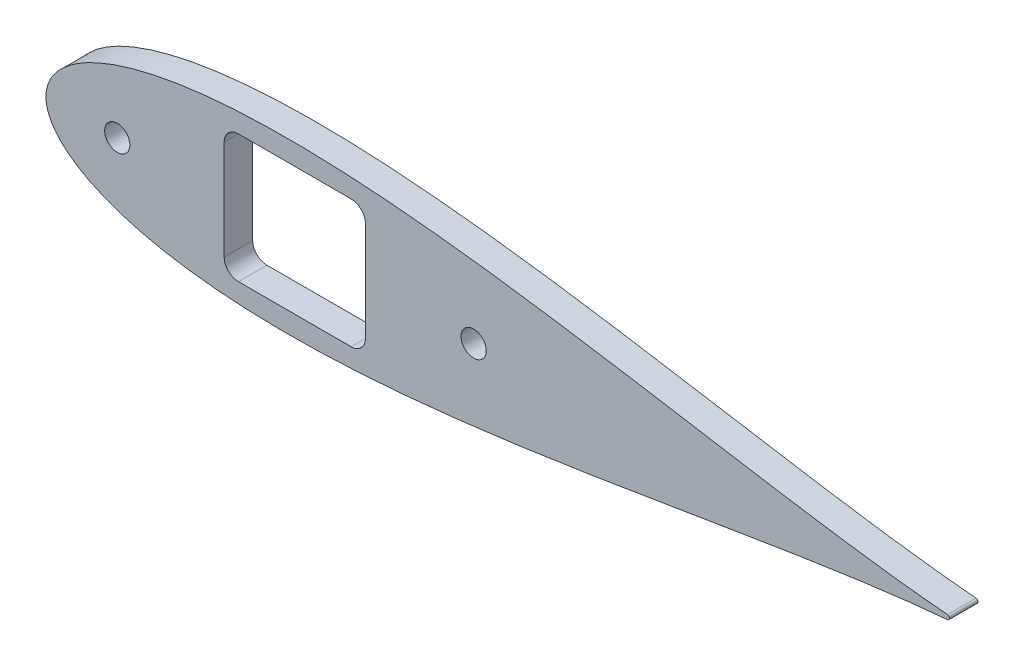
SolidWorks part; units mm, degrees
ref_plane "Front Plane" through (0, 0, 0) normal (0, 0, 1) x (1, 0, 0)
ref_plane "Top Plane" through (0, 0, 0) normal (0, 1, 0) x (1, 0, 0)
ref_plane "Right Plane" through (0, 0, 0) normal (1, 0, 0) x (0, 0, -1)
curve "Curve4"
  spline degree 3 poles (100, 0, 0) (99.8498, 0.0023, 0) (99.4759, 0.008, 0) (99.1023, 0.0238, 0) (98.8789, 0.0332, 0) knots 0 0 0 0 0.401829 1 1 1 1
curve "Curve5"
  spline degree 3 poles (99.3714, -0.0082, 0) (100.2526, 0, 0) (99.3714, 0.0082, 0) (98.8504, 0.035, 0) (97.904, 0.0811, 0) (96.8285, 0.1543, 0) (95.5159, 0.2583, 0) (94.013, 0.3972, 0) (92.313, 0.574, 0) (90.4281, 0.791, 0) (88.3655, 1.0495, 0) (86.1348, 1.3497, 0) (83.7456, 1.691, 0) (81.2082, 2.0715, 0) (78.5335, 2.4886, 0) (75.7326, 2.9386, 0) (72.8172, 3.4168, 0) (69.799, 3.9177, 0) (66.6904, 4.435, 0) (63.5039, 4.9616, 0) (60.2521, 5.4899, 0) (56.948, 6.0119, 0) (53.6049, 6.519, 0) (50.2363, 7.0024, 0) (46.8558, 7.4534, 0) (43.4774, 7.8632, 0) (40.1152, 8.2232, 0) (36.7837, 8.5249, 0) (33.4975, 8.7606, 0) (30.2716, 8.923, 0) (27.1211, 9.0055, 0) (24.0614, 9.0025, 0) (21.108, 8.909, 0) (18.277, 8.7213, 0) (15.5843, 8.4369, 0) (13.0466, 8.0543, 0) (10.6806, 7.5735, 0) (8.5039, 6.996, 0) (6.5349, 6.3253, 0) (4.7933, 5.5673, 0) (3.3001, 4.7321, 0) (2.0777, 3.8366, 0) (1.1467, 2.91, 0) (0.5165, 2.0014, 0) (0.165, 1.1816, 0) (0.0231, 0.524, 0) (-0.0093, 0, 0) (0.0231, -0.524, 0) (0.165, -1.1816, 0) (0.5165, -2.0014, 0) (1.1467, -2.91, 0) (2.0777, -3.8366, 0) (3.3001, -4.7321, 0) (4.7933, -5.5673, 0) (6.5349, -6.3253, 0) (8.5039, -6.996, 0) (10.6806, -7.5735, 0) (13.0466, -8.0543, 0) (15.5843, -8.4369, 0) (18.277, -8.7213, 0) (21.108, -8.909, 0) (24.0614, -9.0025, 0) (27.1211, -9.0055, 0) (30.2716, -8.923, 0) (33.4975, -8.7606, 0) (36.7837, -8.5249, 0) (40.1152, -8.2232, 0) (43.4774, -7.8632, 0) (46.8558, -7.4534, 0) (50.2363, -7.0024, 0) (53.6049, -6.519, 0) (56.948, -6.0119, 0) (60.2521, -5.4899, 0) (63.5039, -4.9616, 0) (66.6904, -4.435, 0) (69.799, -3.9177, 0) (72.8172, -3.4168, 0) (75.7326, -2.9386, 0) (78.5335, -2.4886, 0) (81.2082, -2.0715, 0) (83.7456, -1.691, 0) (86.1348, -1.3497, 0) (88.3655, -1.0495, 0) (90.4281, -0.791, 0) (92.313, -0.574, 0) (94.013, -0.3972, 0) (95.5159, -0.2583, 0) (96.8285, -0.1543, 0) (97.904, -0.0811, 0) (98.8504, -0.035, 0) (99.3714, -0.0082, 0) (100.2526, 0, 0) (99.3714, 0.0082, 0) knots -0.009667 -0.005395 -0.002168 0 0.002168 0.005395 0.009667 0.014967 0.021271 0.028553 0.036781 0.04592 0.055932 0.066773 0.078397 0.090755 0.103793 0.117456 0.131686 0.146422 0.1616 0.177156 0.193024 0.209135 0.225421 0.241812 0.258238 0.274629 0.290914 0.307025 0.322893 0.338448 0.353626 0.368361 0.38259 0.396253 0.40929 0.421647 0.43327 0.444109 0.454119 0.463255 0.471479 0.478755 0.485052 0.490344 0.49461 0.497833 0.5 0.502167 0.50539 0.509656 0.514948 0.521245 0.528521 0.536745 0.545881 0.555891 0.56673 0.578353 0.59071 0.603747 0.61741 0.631639 0.646374 0.661552 0.677107 0.692975 0.709086 0.725371 0.741762 0.758188 0.774579 0.790865 0.806976 0.822844 0.8384 0.853578 0.868314 0.882544 0.896207 0.909245 0.921603 0.933227 0.944068 0.95408 0.963219 0.971447 0.978729 0.985033 0.990333 0.994605 0.997832 1 1.002168 1.005395 1.009667 periodic
sketch "Sketch2" plane through (0, 0, 0) normal (0, 0, 1) x (1, 0, 0)
  line L0 (642.3793, 0) -> (0, 0) construction
  circle A14 centre (642.3793, 0) radius 1.5875 construction
  arc A15 (642.5108, -1.582) -> (642.5108, 1.582) centre (642.3793, 0) ccw
  spline S2 degree 3 poles (666.3448, -0.0547) (672.2538, 0) (666.3448, 0.0547) (662.8509, 0.2344) (656.505, 0.5436) (649.293, 1.0348) (640.4916, 1.7319) (630.4138, 2.6634) (619.0141, 3.8493) (606.375, 5.3044) (592.5439, 7.0376) (577.5855, 9.0506) (561.5643, 11.3389) (544.5497, 13.8907) (526.6141, 16.6877) (507.8326, 19.7051) (488.2827, 22.9117) (468.0444, 26.2704) (447.1994, 29.739) (425.8316, 33.2703) (404.0263, 36.8132) (381.8707, 40.3133) (359.4533, 43.7135) (336.8645, 46.9554) (314.1962, 49.9798) (291.5418, 52.7277) (268.9963, 55.1412) (246.6566, 57.1646) (224.6209, 58.7452) (202.9892, 59.8341) (181.8631, 60.3875) (161.3458, 60.367) (141.542, 59.7399) (122.5581, 58.4818) (104.5023, 56.5743) (87.485, 54.0089) (71.6197, 50.7848) (57.0237, 46.9125) (43.8205, 42.415) (32.1416, 37.3322) (22.1291, 31.7315) (13.9324, 25.7264) (7.6896, 19.5132) (3.4631, 13.4204) (1.1063, 7.9234) (0.1546, 3.5138) (-0.0622, 0) (0.1546, -3.5138) (1.1063, -7.9234) (3.4631, -13.4204) (7.6896, -19.5132) (13.9324, -25.7264) (22.1291, -31.7315) (32.1416, -37.3322) (43.8205, -42.415) (57.0237, -46.9125) (71.6197, -50.7848) (87.485, -54.0089) (104.5023, -56.5743) (122.5581, -58.4818) (141.542, -59.7399) (161.3458, -60.367) (181.8631, -60.3875) (202.9892, -59.8341) (224.6209, -58.7452) (246.6566, -57.1646) (268.9963, -55.1412) (291.5418, -52.7277) (314.1962, -49.9798) (336.8645, -46.9554) (359.4533, -43.7135) (381.8707, -40.3133) (404.0263, -36.8132) (425.8316, -33.2703) (447.1994, -29.739) (468.0444, -26.2704) (488.2827, -22.9117) (507.8326, -19.7051) (526.6141, -16.6877) (544.5497, -13.8907) (561.5643, -11.3389) (577.5855, -9.0506) (592.5439, -7.0376) (606.375, -5.3044) (619.0141, -3.8493) (630.4138, -2.6634) (640.4916, -1.7319) (649.293, -1.0348) (656.505, -0.5436) (662.8509, -0.2344) (666.3448, -0.0547) (672.2538, 0) (666.3448, 0.0547) knots -0.009667 -0.005395 -0.002168 0 0.002168 0.005395 0.009667 0.014967 0.021271 0.028553 0.036781 0.04592 0.055932 0.066773 0.078397 0.090755 0.103793 0.117456 0.131686 0.146422 0.1616 0.177156 0.193024 0.209135 0.225421 0.241812 0.258238 0.274629 0.290914 0.307025 0.322893 0.338448 0.353626 0.368361 0.38259 0.396253 0.40929 0.421647 0.43327 0.444109 0.454119 0.463255 0.471479 0.478755 0.485052 0.490344 0.49461 0.497833 0.5 0.502167 0.50539 0.509656 0.514948 0.521245 0.528521 0.536745 0.545881 0.555891 0.56673 0.578353 0.59071 0.603747 0.61741 0.631639 0.646374 0.661552 0.677107 0.692975 0.709086 0.725371 0.741762 0.758188 0.774579 0.790865 0.806976 0.822844 0.8384 0.853578 0.868314 0.882544 0.896207 0.909245 0.921603 0.933227 0.944068 0.95408 0.963219 0.971447 0.978729 0.985033 0.990333 0.994605 0.997832 1 1.002168 1.005395 1.009667 only from (670.56, 0) to (670.56, 0)
  point P8 (1.2169, -4.6585)
  point P10 (1.2169, 4.6585)
  dimension "D10" = 3.175
extrude "Boss-Extrude1" add sketch "Sketch2" along normal blind 5.4737
extrude "Cut-Extrude4" [suppressed] cut sketch "Sketch7" against normal through all
sketch "Sketch7" plane through (327.9592, -13.7514, 6.35) normal (0, 0, 1) x (1, 0, 0)
  line L1 (-154.9852, -16.7286) -> (-66.0852, -16.7286)
  line L2 (-154.9852, -16.7286) -> (-154.9852, 44.2314)
  line L3 (-154.9852, 44.2314) -> (-66.0852, 44.2314)
  line L4 (-66.0852, -16.7286) -> (-66.0852, 44.2314)
  line L5 (-154.9852, -16.7286) -> (-66.0852, 44.2314) construction
  line L6 (-154.9852, 44.2314) -> (-66.0852, -16.7286) construction
  point P0 (-110.5352, 13.7514)
extrude "Cut-Extrude5" [suppressed] cut sketch "Sketch8" against normal through all
sketch "Sketch8" plane through (327.9592, -13.7514, 6.35) normal (0, 0, 1) x (1, 0, 0)
  circle A0 centre (314.9285, 13.7514) radius 1.2446
scale "Scale1" bodies to scale 101 scale about origin uniform scaling yes scale factor 0.25
sketch "Sketch11" plane through (0, 0, 0) normal (0, 0, -1) x (-1, 0, 0)
  arc A1 (-160.6277, 0.3955) -> (-160.6277, -0.3955) centre (-160.5948, 0) ccw
  arc A2 (-160.6277, 0.3955) -> (-160.6277, -0.3955) centre (-160.5948, 0) ccw
  spline S1 degree 3 poles (2828.4979, -252.2208) (-262.9609, -9.0876) (-204.7793, 3.6945) (-157.6035, -0.6658) (-154.7535, -0.9623) (-151.5937, -1.3261) (-148.136, -1.7594) (-144.3964, -2.2627) (-140.3911, -2.8347) (-136.1374, -3.4727) (-131.6535, -4.1719) (-126.9581, -4.9263) (-122.0707, -5.7279) (-117.0111, -6.5676) (-111.7999, -7.4348) (-106.4579, -8.3176) (-101.0066, -9.2033) (-95.4677, -10.0783) (-89.8633, -10.9284) (-84.2161, -11.7389) (-78.5491, -12.495) (-72.8854, -13.1819) (-67.2491, -13.7853) (-61.6641, -14.2912) (-56.1552, -14.6863) (-50.7473, -14.9585) (-45.4658, -15.0969) (-40.3365, -15.0917) (-35.3855, -14.935) (-30.6395, -14.6204) (-26.1256, -14.1436) (-21.8713, -13.5022) (-17.9049, -12.6962) (-14.2559, -11.7281) (-10.9551, -10.6038) (-8.0354, -9.3331) (-5.5323, -7.9329) (-3.4831, -6.4316) (-1.9224, -4.8783) (-0.8658, -3.3551) (-0.2766, -1.9808) (-0.0387, -0.8784) (0.0155, 0) (-0.0387, 0.8784) (-0.2766, 1.9808) (-0.8658, 3.3551) (-1.9224, 4.8783) (-3.4831, 6.4316) (-5.5323, 7.9329) (-8.0354, 9.3331) (-10.9551, 10.6038) (-14.2559, 11.7281) (-17.9049, 12.6962) (-21.8713, 13.5022) (-26.1256, 14.1436) (-30.6395, 14.6204) (-35.3855, 14.935) (-40.3365, 15.0917) (-45.4658, 15.0969) (-50.7473, 14.9585) (-56.1552, 14.6863) (-61.6641, 14.2912) (-67.2491, 13.7853) (-72.8854, 13.1819) (-78.5491, 12.495) (-84.2161, 11.7389) (-89.8633, 10.9284) (-95.4677, 10.0783) (-101.0066, 9.2033) (-106.4579, 8.3176) (-111.7999, 7.4348) (-117.0111, 6.5676) (-122.0707, 5.7279) (-126.9581, 4.9263) (-131.6535, 4.1719) (-136.1374, 3.4727) (-140.3911, 2.8347) (-144.3964, 2.2627) (-148.136, 1.7594) (-151.5937, 1.3261) (-154.7535, 0.9623) (-157.6035, 0.6658) (-204.7789, -3.6945) (-262.9599, 9.0874) (2828.4114, 252.214) knots -0.371679 -0.371679 -0.371679 -0.371679 0.021271 0.028553 0.036781 0.04592 0.055932 0.066773 0.078397 0.090755 0.103793 0.117456 0.131686 0.146422 0.1616 0.177156 0.193024 0.209135 0.225421 0.241812 0.258238 0.274629 0.290914 0.307025 0.322893 0.338448 0.353626 0.368361 0.38259 0.396253 0.40929 0.421647 0.43327 0.444109 0.454119 0.463255 0.471479 0.478755 0.485052 0.490344 0.49461 0.497833 0.5 0.502167 0.50539 0.509656 0.514948 0.521245 0.528521 0.536745 0.545881 0.555891 0.56673 0.578353 0.59071 0.603747 0.61741 0.631639 0.646374 0.661552 0.677107 0.692975 0.709086 0.725371 0.741762 0.758188 0.774579 0.790865 0.806976 0.822844 0.8384 0.853578 0.868314 0.882544 0.896207 0.909245 0.921603 0.933227 0.944068 0.95408 0.963219 0.971447 0.978729 1.371676 1.371676 1.371676 1.371676 only from (-160.6277, -0.3955) to (-160.6277, 0.3955)
  spline S2 degree 3 poles (-160.6277, -0.3955) (-160.4983, -0.4063) (-159.5234, -0.4884) (-157.6035, -0.6658) (-154.7535, -0.9623) (-151.5937, -1.3261) (-148.136, -1.7594) (-144.3964, -2.2627) (-140.3911, -2.8347) (-136.1374, -3.4727) (-131.6535, -4.1719) (-126.9581, -4.9263) (-122.0707, -5.7279) (-117.0111, -6.5676) (-111.7999, -7.4348) (-106.4579, -8.3176) (-101.0066, -9.2033) (-95.4677, -10.0783) (-89.8633, -10.9284) (-84.2161, -11.7389) (-78.5491, -12.495) (-72.8854, -13.1819) (-67.2491, -13.7853) (-61.6641, -14.2912) (-56.1552, -14.6863) (-50.7473, -14.9585) (-45.4658, -15.0969) (-40.3365, -15.0917) (-35.3855, -14.935) (-30.6395, -14.6204) (-26.1256, -14.1436) (-21.8713, -13.5022) (-17.9049, -12.6962) (-14.2559, -11.7281) (-10.9551, -10.6038) (-8.0354, -9.3331) (-5.5323, -7.9329) (-3.4831, -6.4316) (-1.9224, -4.8783) (-0.8658, -3.3551) (-0.2766, -1.9808) (-0.0387, -0.8784) (0.0155, 0) (-0.0387, 0.8784) (-0.2766, 1.9808) (-0.8658, 3.3551) (-1.9224, 4.8783) (-3.4831, 6.4316) (-5.5323, 7.9329) (-8.0354, 9.3331) (-10.9551, 10.6038) (-14.2559, 11.7281) (-17.9049, 12.6962) (-21.8713, 13.5022) (-26.1256, 14.1436) (-30.6395, 14.6204) (-35.3855, 14.935) (-40.3365, 15.0917) (-45.4658, 15.0969) (-50.7473, 14.9585) (-56.1552, 14.6863) (-61.6641, 14.2912) (-67.2491, 13.7853) (-72.8854, 13.1819) (-78.5491, 12.495) (-84.2161, 11.7389) (-89.8633, 10.9284) (-95.4677, 10.0783) (-101.0066, 9.2033) (-106.4579, 8.3176) (-111.7999, 7.4348) (-117.0111, 6.5676) (-122.0707, 5.7279) (-126.9581, 4.9263) (-131.6535, 4.1719) (-136.1374, 3.4727) (-140.3911, 2.8347) (-144.3964, 2.2627) (-148.136, 1.7594) (-151.5937, 1.3261) (-154.7535, 0.9623) (-157.6035, 0.6658) (-159.5234, 0.4884) (-160.4983, 0.4063) (-160.6277, 0.3955) knots 0.020157 0.020157 0.020157 0.020157 0.021271 0.028553 0.036781 0.04592 0.055932 0.066773 0.078397 0.090755 0.103793 0.117456 0.131686 0.146422 0.1616 0.177156 0.193024 0.209135 0.225421 0.241812 0.258238 0.274629 0.290914 0.307025 0.322893 0.338448 0.353626 0.368361 0.38259 0.396253 0.40929 0.421647 0.43327 0.444109 0.454119 0.463255 0.471479 0.478755 0.485052 0.490344 0.49461 0.497833 0.5 0.502167 0.50539 0.509656 0.514948 0.521245 0.528521 0.536745 0.545881 0.555891 0.56673 0.578353 0.59071 0.603747 0.61741 0.631639 0.646374 0.661552 0.677107 0.692975 0.709086 0.725371 0.741762 0.758188 0.774579 0.790865 0.806976 0.822844 0.8384 0.853578 0.868314 0.882544 0.896207 0.909245 0.921603 0.933227 0.944068 0.95408 0.963219 0.971447 0.978729 0.979843 0.979843 0.979843 0.979843
  dimension "D1" = 0
extrude "Boss-Extrude2" add sketch "Sketch11" against normal blind 5.08
sketch "Sketch10" plane through (0, 0, 0) normal (0, 0, 1) x (1, 0, 0)
  line L1 (31.75, -11.4046) -> (56.9172, -11.4046)
  line L2 (31.75, -11.4046) -> (31.75, 11.4046)
  line L3 (31.75, 11.4046) -> (56.9172, 11.4046)
  line L4 (56.9172, -11.4046) -> (56.9172, 11.4046)
  line L5 (31.75, -11.4046) -> (56.9172, 11.4046) construction
  line L6 (31.75, 11.4046) -> (56.9172, -11.4046) construction
  arc A2 (160.6277, -0.3955) -> (160.6277, 0.3955) centre (160.5948, 0) ccw
  arc A3 (160.6277, -0.3955) -> (160.6277, 0.3955) centre (160.5948, 0) ccw construction
  spline S1 degree 3 poles (-835.1283, 91.8902) (230.3012, 3.1197) (191.4077, -2.4586) (157.6035, 0.6658) (154.7535, 0.9623) (151.5937, 1.3261) (148.136, 1.7594) (144.3964, 2.2627) (140.3911, 2.8347) (136.1374, 3.4727) (131.6535, 4.1719) (126.9581, 4.9263) (122.0707, 5.7279) (117.0111, 6.5676) (111.7999, 7.4348) (106.4579, 8.3176) (101.0066, 9.2033) (95.4677, 10.0783) (89.8633, 10.9284) (84.2161, 11.7389) (78.5491, 12.495) (72.8854, 13.1819) (67.2491, 13.7853) (61.6641, 14.2912) (56.1552, 14.6863) (50.7473, 14.9585) (45.4658, 15.0969) (40.3365, 15.0917) (35.3855, 14.935) (30.6395, 14.6204) (26.1256, 14.1436) (21.8713, 13.5022) (17.9049, 12.6962) (14.2559, 11.7281) (10.9551, 10.6038) (8.0354, 9.3331) (5.5323, 7.9329) (3.4831, 6.4316) (1.9224, 4.8783) (0.8658, 3.3551) (0.2766, 1.9808) (0.0387, 0.8784) (-0.0155, 0) (0.0387, -0.8784) (0.2766, -1.9808) (0.8658, -3.3551) (1.9224, -4.8783) (3.4831, -6.4316) (5.5323, -7.9329) (8.0354, -9.3331) (10.9551, -10.6038) (14.2559, -11.7281) (17.9049, -12.6962) (21.8713, -13.5022) (26.1256, -14.1436) (30.6395, -14.6204) (35.3855, -14.935) (40.3365, -15.0917) (45.4658, -15.0969) (50.7473, -14.9585) (56.1552, -14.6863) (61.6641, -14.2912) (67.2491, -13.7853) (72.8854, -13.1819) (78.5491, -12.495) (84.2161, -11.7389) (89.8633, -10.9284) (95.4677, -10.0783) (101.0066, -9.2033) (106.4579, -8.3176) (111.7999, -7.4348) (117.0111, -6.5676) (122.0707, -5.7279) (126.9581, -4.9263) (131.6535, -4.1719) (136.1374, -3.4727) (140.3911, -2.8347) (144.3964, -2.2627) (148.136, -1.7594) (151.5937, -1.3261) (154.7535, -0.9623) (157.6035, -0.6658) (191.4079, 2.4586) (230.3016, -3.1198) (-835.1445, -91.8915) knots -0.255905 -0.255905 -0.255905 -0.255905 0.021271 0.028553 0.036781 0.04592 0.055932 0.066773 0.078397 0.090755 0.103793 0.117456 0.131686 0.146422 0.1616 0.177156 0.193024 0.209135 0.225421 0.241812 0.258238 0.274629 0.290914 0.307025 0.322893 0.338448 0.353626 0.368361 0.38259 0.396253 0.40929 0.421647 0.43327 0.444109 0.454119 0.463255 0.471479 0.478755 0.485052 0.490344 0.49461 0.497833 0.5 0.502167 0.50539 0.509656 0.514948 0.521245 0.528521 0.536745 0.545881 0.555891 0.56673 0.578353 0.59071 0.603747 0.61741 0.631639 0.646374 0.661552 0.677107 0.692975 0.709086 0.725371 0.741762 0.758188 0.774579 0.790865 0.806976 0.822844 0.8384 0.853578 0.868314 0.882544 0.896207 0.909245 0.921603 0.933227 0.944068 0.95408 0.963219 0.971447 0.978729 1.255906 1.255906 1.255906 1.255906 only from (160.6277, 0.3955) to (160.6277, -0.3955)
  point P0 (44.3336, 0)
  dimension "D1" = 25.1672
  dimension "D2" = 31.75
  dimension "D5" = 22.8092
  dimension "D3" = 0
extrude "Cut-Extrude6" cut sketch "Sketch10" along normal through all
fillet "Fillet1" radius 2.54 4 edges at (56.9172, -11.4046, 2.54) (31.75, -11.4046, 2.54) (31.75, 11.4046, 2.54) (56.9172, 11.4046, 2.54)
hole_wizard "#8 Clearance Hole1" positions "Sketch12" profile "Sketch13" hole size "#8" standard "ANSI Inch" end condition through all
sketch "Sketch12" plane through (0, 0, 5.08) normal (0, 0, 1) x (1, 0, 0)
  line L0 (76.2, 0) -> (0, 0) construction
  line L2 (31.75, 8.8646) -> (31.75, -8.8646) construction
  point P0 (12.7, 0)
  point P2 (76.2, 0)
  dimension "D1" = 19.05
  dimension "D2" = 44.45
sketch "Sketch13" plane through (12.7, 0, 5.08) normal (1, 0, 0) x (0, -1, 0)
  line L0 (0, 0) -> (0, 5.08)
  line L1 (0, 5.08) -> (2.2479, 5.08)
  line L2 (2.2479, 5.08) -> (2.2479, 0)
  line L5 (2.2479, 0) -> (0, 0)
  line L11 (0, -6.35) -> (0, 107.95) construction
  dimension "Thru Hole Dia." = 4.4958
  dimension "Thru Hole Depth" = 5.08
sketch "Sketch14" [suppressed] plane through (0, 0, 5.08) normal (0, 0, 1) x (1, 0, 0)
  line L0 (67.0772, 8.7068) -> (67.0772, -8.7068)
  line L1 (67.0772, -8.7068) -> (87.5173, -6.1829)
  line L2 (87.5173, -6.1829) -> (87.5173, 6.1829)
  line L3 (87.5173, 6.1829) -> (67.0772, 8.7068)
  line L4 (67.0772, 0) -> (87.5173, 0) construction
  line L5 (56.9172, -8.8646) -> (56.9172, 8.8646) construction
  spline S0 degree 3 poles (160.6277, -0.3955) (160.4983, -0.4063) (159.5234, -0.4884) (157.6035, -0.6658) (154.7535, -0.9623) (151.5937, -1.3261) (148.136, -1.7594) (144.3964, -2.2627) (140.3911, -2.8347) (136.1374, -3.4727) (131.6535, -4.1719) (126.9581, -4.9263) (122.0707, -5.7279) (117.0111, -6.5676) (111.7999, -7.4348) (106.4579, -8.3176) (101.0066, -9.2033) (95.4677, -10.0783) (89.8633, -10.9284) (84.2161, -11.7389) (78.5491, -12.495) (72.8854, -13.1819) (67.2491, -13.7853) (61.6641, -14.2912) (56.1552, -14.6863) (50.7473, -14.9585) (45.4658, -15.0969) (40.3365, -15.0917) (35.3855, -14.935) (30.6395, -14.6204) (26.1256, -14.1436) (21.8713, -13.5022) (17.9049, -12.6962) (14.2559, -11.7281) (10.9551, -10.6038) (8.0354, -9.3331) (5.5323, -7.9329) (3.4831, -6.4316) (1.9224, -4.8783) (0.8658, -3.3551) (0.2766, -1.9808) (0.0387, -0.8784) (-0.0155, 0) (0.0387, 0.8784) (0.2766, 1.9808) (0.8658, 3.3551) (1.9224, 4.8783) (3.4831, 6.4316) (5.5323, 7.9329) (8.0354, 9.3331) (10.9551, 10.6038) (14.2559, 11.7281) (17.9049, 12.6962) (21.8713, 13.5022) (26.1256, 14.1436) (30.6395, 14.6204) (35.3855, 14.935) (40.3365, 15.0917) (45.4658, 15.0969) (50.7473, 14.9585) (56.1552, 14.6863) (61.6641, 14.2912) (67.2491, 13.7853) (72.8854, 13.1819) (78.5491, 12.495) (84.2161, 11.7389) (89.8633, 10.9284) (95.4677, 10.0783) (101.0066, 9.2033) (106.4579, 8.3176) (111.7999, 7.4348) (117.0111, 6.5676) (122.0707, 5.7279) (126.9581, 4.9263) (131.6535, 4.1719) (136.1374, 3.4727) (140.3911, 2.8347) (144.3964, 2.2627) (148.136, 1.7594) (151.5937, 1.3261) (154.7535, 0.9623) (157.6035, 0.6658) (159.5234, 0.4884) (160.4983, 0.4063) (160.6277, 0.3955) knots 0.020157 0.020157 0.020157 0.020157 0.021271 0.028553 0.036781 0.04592 0.055932 0.066773 0.078397 0.090755 0.103793 0.117456 0.131686 0.146422 0.1616 0.177156 0.193024 0.209135 0.225421 0.241812 0.258238 0.274629 0.290914 0.307025 0.322893 0.338448 0.353626 0.368361 0.38259 0.396253 0.40929 0.421647 0.43327 0.444109 0.454119 0.463255 0.471479 0.478755 0.485052 0.490344 0.49461 0.497833 0.5 0.502167 0.50539 0.509656 0.514948 0.521245 0.528521 0.536745 0.545881 0.555891 0.56673 0.578353 0.59071 0.603747 0.61741 0.631639 0.646374 0.661552 0.677107 0.692975 0.709086 0.725371 0.741762 0.758188 0.774579 0.790865 0.806976 0.822844 0.8384 0.853578 0.868314 0.882544 0.896207 0.909245 0.921603 0.933227 0.944068 0.95408 0.963219 0.971447 0.978729 0.979843 0.979843 0.979843 0.979843 construction
  point P6 (87.5173, 11.2629)
  point P9 (56.9172, 0)
  point P10 (67.0772, 13.7868)
  point P11 (93.8673, -10.3187)
  point P20 (93.8673, 10.3188)
  dimension "D1" = 5.08
  dimension "D2" = 5.08
  dimension "D3" = 20.6375
  dimension "D4" = 10.16
  dimension "D5" = 6.35
extrude "Cut-Extrude7" [suppressed] cut sketch "Sketch14" against normal through all
fillet "Fillet2" [suppressed] radius 5.08
equation "\"0.5n\"=0"
equation "\"D2@Sketch14\"=\"D1@Sketch14\""
equation "\"D1@Sketch10\"=0.898/cos(25deg)"
